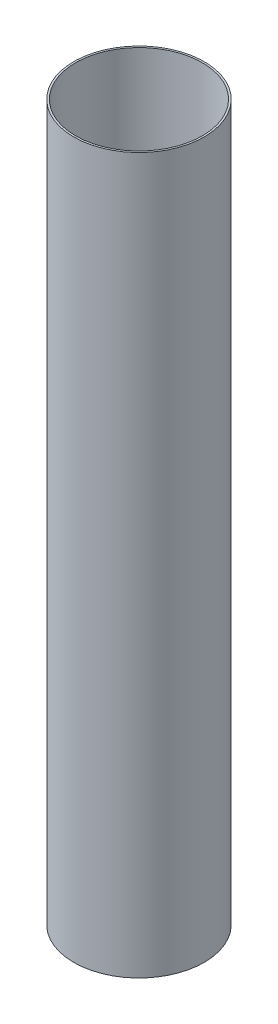
SolidWorks part; units mm, degrees
ref_plane "Front Plane" through (0, 0, 0) normal (0, 0, 1) x (1, 0, 0)
ref_plane "Top Plane" through (0, 0, 0) normal (0, 1, 0) x (1, 0, 0)
ref_plane "Right Plane" through (0, 0, 0) normal (1, 0, 0) x (0, 0, -1)
sketch "Sketch2" plane through (0, 0, 0) normal (0, 1, 0) x (1, 0, 0)
  circle A0 centre (0, 0) radius 51
  circle A1 centre (0, 0) radius 49.55
  dimension "D1" = 99.1
  dimension "D2" = 102
extrude "Boss-Extrude1" add sketch "Sketch2" along normal blind 558.8
